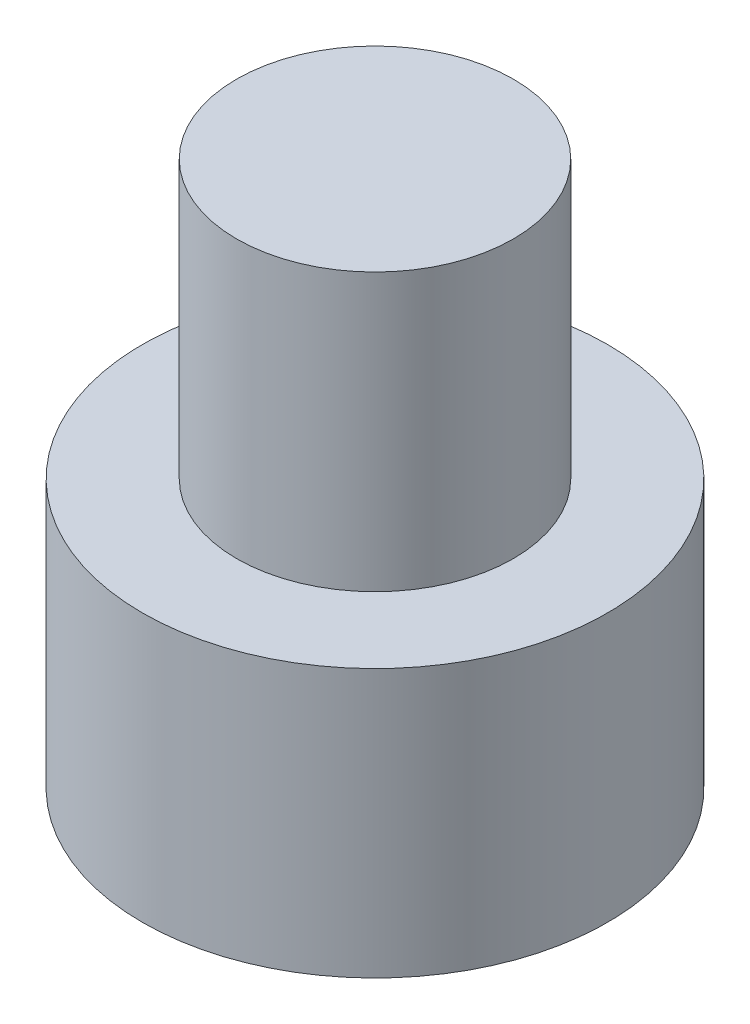
SolidWorks part; units mm, degrees
ref_plane "前视基准面" through (0, 0, 0) normal (0, 0, 1) x (1, 0, 0)
ref_plane "上视基准面" through (0, 0, 0) normal (0, 1, 0) x (1, 0, 0)
ref_plane "右视基准面" through (0, 0, 0) normal (1, 0, 0) x (0, 0, -1)
sketch "草图1" plane through (0, 0, 0) normal (0, 1, 0) x (1, 0, 0)
  circle A0 centre (0, 0) radius 4.2
extrude "凸台-拉伸1" add sketch "草图1" along normal blind 4.84
sketch "草图2" plane through (0, 4.84, 0) normal (0, 1, 0) x (1, 0, 0)
  circle A0 centre (0, 0) radius 2.5
extrude "凸台-拉伸2" add sketch "草图2" along normal blind 5
sketch "草图3" plane through (0, 0, 0) normal (0, -1, 0) x (1, 0, 0)
  line L1 (2.3, 0) -> (1.15, 1.9919)
  line L2 (1.15, 1.9919) -> (-1.15, 1.9919)
  line L3 (-1.15, 1.9919) -> (-2.3, 0)
  line L4 (-2.3, 0) -> (-1.15, -1.9919)
  line L5 (-1.15, -1.9919) -> (1.15, -1.9919)
  line L6 (1.15, -1.9919) -> (2.3, 0)
  circle A0 centre (0, 0) radius 1.9919 construction
extrude "切除-拉伸1" cut sketch "草图3" against normal blind 3.4
